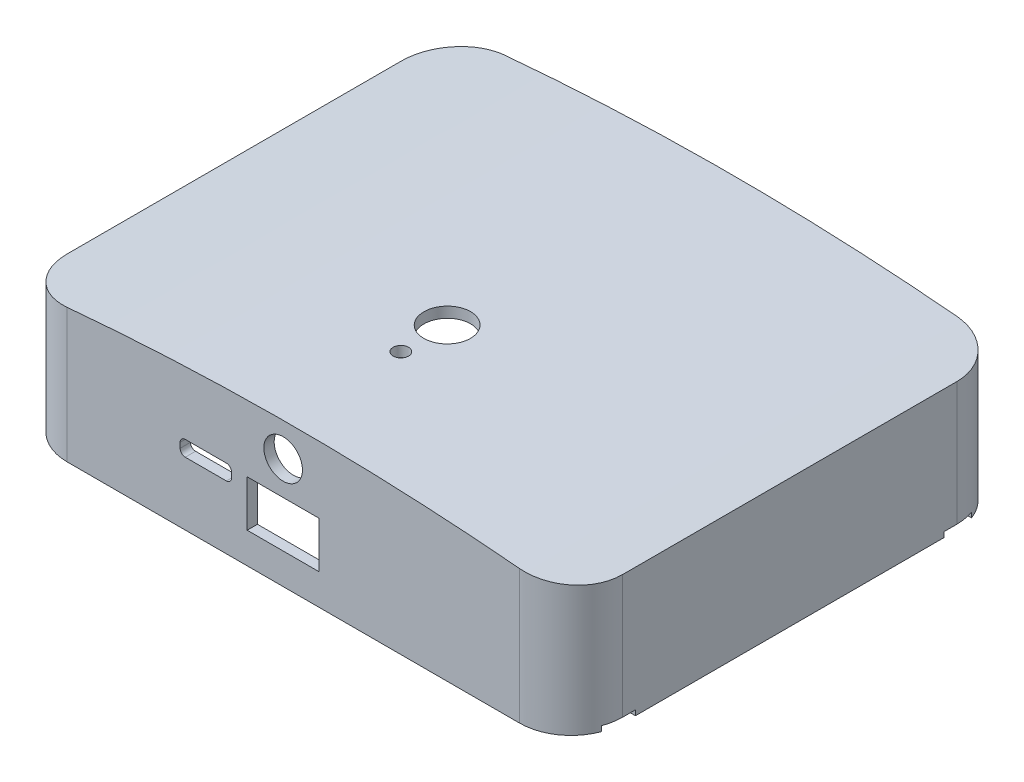
SolidWorks part; units mm, degrees
ref_plane "Front Plane" through (0, 0, 0) normal (0, 0, 1) x (1, 0, 0)
ref_plane "Top Plane" through (0, 0, 0) normal (0, 1, 0) x (1, 0, 0)
ref_plane "Right Plane" through (0, 0, 0) normal (1, 0, 0) x (0, 0, -1)
ref_plane "Plane2" through (0, 0, -85) normal (0, 0, 1) x (1, 0, 0)
ref_plane "Plane3" through (0, 2, 0) normal (0, 1, 0) x (1, 0, 0)
sketch "Sketch10" plane through (0, 2, 0) normal (0, 1, 0) x (1, 0, 0)
  line L0 (57.999, 83) -> (-30.001, 83)
  line L1 (-38.001, 75) -> (-38.001, 10)
  line L2 (-30.001, 2) -> (57.999, 2)
  line L3 (65.999, 10) -> (65.999, 75)
  line L12 (67.999, 10) -> (67.999, 75)
  line L13 (-30.001, 0) -> (57.999, 0)
  line L14 (-40.001, 75) -> (-40.001, 10)
  line L15 (57.999, 85) -> (-30.001, 85)
  arc A0 (65.999, 75) -> (57.999, 83) centre (57.999, 75) ccw
  arc A1 (-30.001, 83) -> (-38.001, 75) centre (-30.001, 75) ccw
  arc A2 (-38.001, 10) -> (-30.001, 2) centre (-30.001, 10) ccw
  arc A3 (57.999, 2) -> (65.999, 10) centre (57.999, 10) ccw
  arc A12 (67.999, 75) -> (57.999, 85) centre (57.999, 75) ccw
  arc A13 (57.999, 0) -> (67.999, 10) centre (57.999, 10) ccw
  arc A14 (-40.001, 10) -> (-30.001, 0) centre (-30.001, 10) ccw
  arc A15 (-30.001, 85) -> (-40.001, 75) centre (-30.001, 75) ccw
  dimension "D1" = 2
extrude "Boss-Extrude5" add sketch "Sketch10" along normal blind 42
sketch "Sketch20" plane through (0, 0, 0) normal (0, 0, 1) x (1, 0, 0)
  line L0 (-40.001, 25) -> (67.999, 25) construction
  line L1 (-32.001, 5) -> (18.999, 5) construction
  line L2 (-32.001, 5) -> (-32.001, 25) construction
  line L3 (-32.001, 25) -> (18.999, 25) construction
  line L4 (18.999, 5) -> (18.999, 25) construction
  line L5 (-40.001, 44) -> (-40.001, 2) construction
  line L6 (67.999, 44) -> (67.999, 2) construction
  line L7 (13.999, 25) -> (13.999, 27.03) construction
  line L9 (13.999, 25) -> (13.999, 28.9912) construction
  line L10 (13.999, 25) -> (13.999, 30.9628) construction
  line L11 (-40.001, 25) -> (-40.001, 27.03)
  line L12 (67.999, 25) -> (67.999, 27.03)
  line L13 (13.999, 25) -> (13.999, 27.9584) construction
  line L14 (13.999, 25) -> (13.999, 30.0146) construction
  spline S1 degree 2 poles (-40.001, 25) (13.999, 30.9168) (67.999, 25) knots 0 0 0 1 1 1
  spline S2 degree 2 poles (67.999, 27.03) (13.999, 32.9992) (-40.001, 27.03) knots 0 0 0 1 1 1
  dimension "D1" = 20
sketch "Sketch22" plane through (0, 0, 0) normal (0, 0, 1) x (1, 0, 0)
  line L0 (67.999, 44) -> (67.999, 2) construction
  line L1 (67.999, 44) -> (57.999, 44) construction
  line L2 (-30.001, 44) -> (-40.001, 44) construction
  line L3 (-30.001, 44) -> (57.999, 44) construction
  line L4 (-40.001, 44) -> (-40.001, 2) construction
  line L5 (67.999, 44) -> (67.999, 25)
  line L6 (67.999, 44) -> (57.999, 44)
  line L7 (-30.001, 44) -> (-40.001, 44)
  line L8 (-30.001, 44) -> (57.999, 44)
  line L9 (-40.001, 44) -> (-40.001, 25)
  line L10 (-40.001, 25) -> (67.999, 25) construction
  line L11 (13.999, 25) -> (13.999, 28.0496) construction
  spline S0 degree 2 poles (-40.001, 25) (13.999, 31.0992) (67.999, 25) knots 0 0 0 1 1 1
extrude "Cut-Extrude6" cut sketch "Sketch22" against normal blind 95
extrude "Boss-Extrude8" add sketch "Sketch20" against normal blind 85
sketch "Sketch23" plane through (0, 2, 0) normal (0, -1, 0) x (1, 0, 0)
  line L0 (-40.001, -75) -> (-40.001, -85) construction
  line L1 (-40.001, -85) -> (-30.001, -85) construction
  line L2 (57.999, -85) -> (67.999, -85) construction
  line L3 (67.999, -85) -> (67.999, -75) construction
  line L4 (67.999, -10) -> (67.999, 0) construction
  line L5 (67.999, 0) -> (57.999, 0) construction
  line L6 (-30.001, 0) -> (-40.001, 0) construction
  line L7 (-40.001, 0) -> (-40.001, -10) construction
  line L8 (-40.001, -75) -> (-40.001, -85)
  line L9 (-40.001, -85) -> (-30.001, -85)
  line L10 (57.999, -85) -> (67.999, -85)
  line L11 (67.999, -85) -> (67.999, -75)
  line L12 (67.999, -10) -> (67.999, 0)
  line L13 (67.999, 0) -> (57.999, 0)
  line L14 (-30.001, 0) -> (-40.001, 0)
  line L15 (-40.001, 0) -> (-40.001, -10)
  arc A0 (-40.001, -75) -> (-30.001, -85) centre (-30.001, -75) ccw construction
  arc A1 (57.999, -85) -> (67.999, -75) centre (57.999, -75) ccw construction
  arc A2 (67.999, -10) -> (57.999, 0) centre (57.999, -10) ccw construction
  arc A3 (-30.001, 0) -> (-40.001, -10) centre (-30.001, -10) ccw construction
  arc A4 (-40.001, -75) -> (-30.001, -85) centre (-30.001, -75) ccw
  arc A5 (57.999, -85) -> (67.999, -75) centre (57.999, -75) ccw
  arc A6 (67.999, -10) -> (57.999, 0) centre (57.999, -10) ccw
  arc A7 (-30.001, 0) -> (-40.001, -10) centre (-30.001, -10) ccw
extrude "Cut-Extrude7" cut sketch "Sketch23" against normal blind 85
sketch "Sketch26" plane through (0, 0, 0) normal (0, 0, 1) x (1, 0, 0)
  line L0 (-32.001, 5) -> (18.999, 5) construction
  line L1 (-40.001, 14.515) -> (67.999, 14.515) construction
  line L2 (-40.001, 27.03) -> (-40.001, 2) construction
  line L3 (67.999, 27.03) -> (67.999, 2) construction
  line L4 (13.999, 14.515) -> (13.999, 36.3942) construction
  line L5 (18.999, 5) -> (18.999, 26.3407) construction
  line L6 (4.999, 17) -> (18.999, 17)
  line L7 (4.999, 17) -> (4.999, 8)
  line L8 (4.999, 8) -> (18.999, 8)
  line L9 (18.999, 17) -> (18.999, 8)
  line L10 (11.999, 17) -> (11.999, 30.0105) construction
  circle A0 centre (11.999, 23.5) radius 3.75
  parabola Q0 (57.999, 28.033) -> (-30.001, 28.033) focus (13.999, -214.2381) apex (13.999, 30.0146) construction
  dimension "D6" = 7.5
  dimension "D1" = 14
  dimension "D2" = 9
  dimension "D3" = 0
  dimension "D4" = 3
  dimension "D5" = 6.5
extrude "Cut-Extrude9" cut sketch "Sketch26" against normal blind 15 contours L9 L6 L7 L8 | A0
sketch "Sketch28" plane through (0, 2, 0) normal (0, -1, 0) x (1, 0, 0)
  line L4 (-30.001, -85) -> (57.999, -85)
  line L5 (67.999, -75) -> (67.999, -10)
  line L6 (57.999, 0) -> (-30.001, 0)
  line L7 (-40.001, -10) -> (-40.001, -75)
  line L9 (67.999, -75) -> (67.999, -72.5)
  line L11 (-40.001, -10) -> (-40.001, -12.5)
  line L18 (63.999, -12.5) -> (67.999, -12.5)
  line L19 (67.3665, -6.5) -> (63.999, -6.5)
  line L20 (63.999, -78.5) -> (67.3665, -78.5)
  line L21 (-40.001, -72.5) -> (-40.001, -75)
  line L22 (67.999, -72.5) -> (63.999, -72.5)
  line L23 (-39.3685, -78.5) -> (-36.001, -78.5)
  line L24 (-36.001, -72.5) -> (-40.001, -72.5)
  line L26 (-40.001, -12.5) -> (-36.001, -12.5)
  line L27 (-36.001, -6.5) -> (-39.3685, -6.5)
  line L28 (67.999, -12.5) -> (67.999, -10)
  arc A4 (57.999, -85) -> (67.999, -75) centre (57.999, -75) ccw
  arc A5 (67.999, -10) -> (57.999, 0) centre (57.999, -10) ccw
  arc A6 (-30.001, 0) -> (-40.001, -10) centre (-30.001, -10) ccw
  arc A7 (-40.001, -75) -> (-30.001, -85) centre (-30.001, -75) ccw
  arc A8 (67.3665, -78.5) -> (67.999, -75) centre (57.999, -75) ccw
  arc A9 (67.999, -10) -> (67.3665, -6.5) centre (57.999, -10) ccw
  arc A10 (-39.3685, -6.5) -> (-40.001, -10) centre (-30.001, -10) ccw
  arc A11 (-40.001, -75) -> (-39.3685, -78.5) centre (-30.001, -75) ccw
  arc A16 (63.999, -6.5) -> (63.999, -12.5) centre (63.999, -9.5) ccw
  arc A19 (63.999, -72.5) -> (63.999, -78.5) centre (63.999, -75.5) ccw
  arc A21 (-36.001, -78.5) -> (-36.001, -72.5) centre (-36.001, -75.5) ccw
  arc A23 (-36.001, -12.5) -> (-36.001, -6.5) centre (-36.001, -9.5) ccw
  dimension "D1" = 0
extrude "Boss-Extrude9" add sketch "Sketch28" against normal blind 15
sketch "Sketch29" plane through (0, 2, 0) normal (0, -1, 0) x (1, 0, 0)
  line L14 (67.999, -72.5) -> (67.999, -75)
  line L15 (63.999, -12.5) -> (67.999, -12.5)
  line L16 (67.3665, -6.5) -> (63.999, -6.5)
  line L17 (-40.001, -12.5) -> (-40.001, -10)
  line L18 (67.999, -10) -> (67.999, -12.5)
  line L19 (67.999, -72.5) -> (63.999, -72.5)
  line L20 (63.999, -78.5) -> (67.3665, -78.5)
  line L22 (-39.3685, -78.5) -> (-36.001, -78.5)
  line L23 (-36.001, -72.5) -> (-40.001, -72.5)
  line L24 (-40.001, -75) -> (-40.001, -72.5)
  line L26 (-40.001, -12.5) -> (-36.001, -12.5)
  line L27 (-36.001, -6.5) -> (-39.3685, -6.5)
  arc A12 (67.999, -10) -> (67.3665, -6.5) centre (57.999, -10) ccw
  arc A14 (63.999, -6.5) -> (63.999, -12.5) centre (63.999, -9.5) ccw
  arc A16 (67.3665, -78.5) -> (67.999, -75) centre (57.999, -75) ccw
  arc A17 (63.999, -72.5) -> (63.999, -78.5) centre (63.999, -75.5) ccw
  arc A18 (-40.001, -75) -> (-39.3685, -78.5) centre (-30.001, -75) ccw
  arc A20 (-36.001, -78.5) -> (-36.001, -72.5) centre (-36.001, -75.5) ccw
  arc A22 (-39.3685, -6.5) -> (-40.001, -10) centre (-30.001, -10) ccw
  arc A23 (-36.001, -12.5) -> (-36.001, -6.5) centre (-36.001, -9.5) ccw
extrude "Cut-Extrude11" cut sketch "Sketch29" against normal blind 1
sketch "Sketch30" plane through (0, 3, 0) normal (0, -1, 0) x (1, 0, 0)
  circle A0 centre (-36.001, -9.5) radius 1.4
  circle A1 centre (63.999, -9.5) radius 1.4
  circle A2 centre (63.999, -75.5) radius 1.4
  circle A3 centre (-36.001, -75.5) radius 1.4
extrude "Cut-Extrude12" cut sketch "Sketch30" against normal blind 15
sketch "Sketch31" plane through (-40.001, 0, 0) normal (-1, 0, 0) x (0, 0, 1)
  line L4 (-63.5, 13) -> (-53.5, 13)
  line L5 (-52.5, 19) -> (-52.5, 14)
  line L6 (-63.5, 20) -> (-53.5, 20)
  line L7 (-64.5, 19) -> (-64.5, 14)
  arc A4 (-64.5, 14) -> (-63.5, 13) centre (-63.5, 14) ccw
  arc A5 (-53.5, 13) -> (-52.5, 14) centre (-53.5, 14) ccw
  arc A6 (-52.5, 19) -> (-53.5, 20) centre (-53.5, 19) ccw
  arc A7 (-63.5, 20) -> (-64.5, 19) centre (-63.5, 19) ccw
extrude "Cut-Extrude17" cut sketch "Sketch31" against normal blind 3
sketch "Sketch32" plane through (0, 2, 0) normal (0, -1, 0) x (1, 0, 0)
  line L0 (-30.001, -2) -> (57.999, -2) construction
  circle A0 centre (11.8847, -32) radius 4.5284
  dimension "D1" = 30
extrude "Cut-Extrude18" cut sketch "Sketch32" against normal blind 42
sketch "Sketch33" plane through (0, 2, 0) normal (0, -1, 0) x (1, 0, 0)
  line L0 (-30.001, -2) -> (57.999, -2) construction
  circle A0 centre (11.8847, -23) radius 1.5
  dimension "D1" = 3
  dimension "D2" = 21
extrude "Cut-Extrude19" cut sketch "Sketch33" against normal blind 42
sketch "Sketch34" plane through (0, 0, 0) normal (0, 0, 1) x (1, 0, 0)
  line L1 (-7.039, 17.277) -> (0.961, 17.277)
  line L2 (-8.039, 16.277) -> (-8.039, 15.277)
  line L3 (-7.039, 14.277) -> (0.961, 14.277)
  line L4 (1.961, 16.277) -> (1.961, 15.277)
  arc A0 (1.961, 15.277) -> (0.961, 14.277) centre (0.961, 15.277) cw
  arc A1 (1.961, 16.277) -> (0.961, 17.277) centre (0.961, 16.277) ccw
  arc A2 (-7.039, 14.277) -> (-8.039, 15.277) centre (-7.039, 15.277) cw
  arc A3 (-8.039, 16.277) -> (-7.039, 17.277) centre (-7.039, 16.277) cw
  point P8 (1.961, 17.277)
  point P11 (-8.039, 14.277)
  point P14 (-8.039, 17.277)
  dimension "D3" = 1
  dimension "D1" = 10
  dimension "D2" = 3
extrude "Cut-Extrude20" cut sketch "Sketch34" against normal blind 3 contours L4 L1 L2 L3
